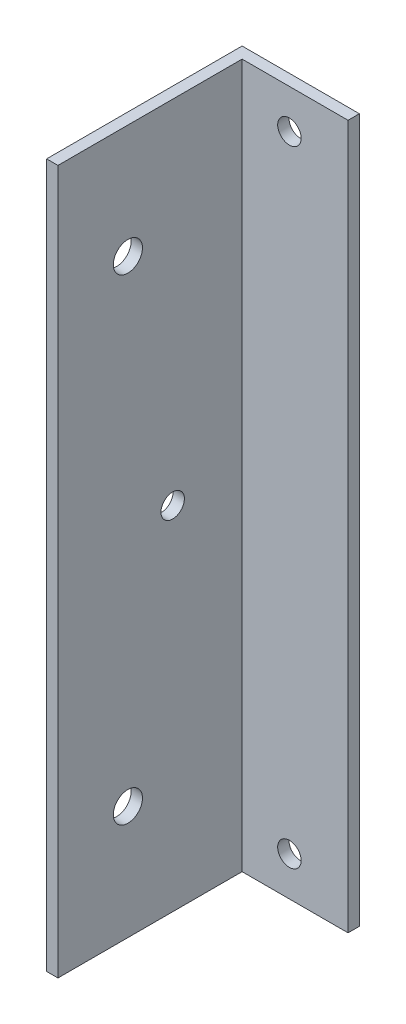
SolidWorks part; units mm, degrees
ref_plane "Front Plane" through (0, 0, 0) normal (0, 0, 1) x (1, 0, 0)
ref_plane "Top Plane" through (0, 0, 0) normal (0, 1, 0) x (1, 0, 0)
ref_plane "Right Plane" through (0, 0, 0) normal (1, 0, 0) x (0, 0, -1)
sketch "Sketch1" plane through (0, 0, 0) normal (0, 0, 1) x (1, 0, 0)
  line L1 (-7.5, 45) -> (7.5, 45)
  line L2 (-7.5, 45) -> (-7.5, -45)
  line L3 (-7.5, -45) -> (7.5, -45)
  line L4 (7.5, 45) -> (7.5, -45)
  line L5 (-7.5, 45) -> (7.5, -45) construction
  line L6 (-7.5, -45) -> (7.5, 45) construction
  point P0 (0, 0)
  dimension "D1" = 15
  dimension "D2" = 90
extrude "Boss-Extrude1" add sketch "Sketch1" along normal blind 1.45
sketch "Sketch2" plane through (0, 0, 1.45) normal (0, 0, 1) x (1, 0, 0)
  line L0 (-7.5, -45) -> (7.5, -45) construction
  line L1 (-7.5, 45) -> (-6.05, 45)
  line L2 (-7.5, 45) -> (-7.5, -45)
  line L3 (-7.5, -45) -> (-6.05, -45)
  line L4 (-6.05, 45) -> (-6.05, -45)
  dimension "D1" = 1.45
extrude "Boss-Extrude2" add sketch "Sketch2" along normal blind 23.55
sketch "Sketch3" plane through (0, 0, 0) normal (0, 0, -1) x (-1, 0, 0)
  line L0 (-7.5, 45) -> (7.5, 45) construction
  line L1 (7.5, -45) -> (-7.5, -45) construction
  circle A0 centre (0, 40) radius 1.5
  circle A1 centre (0, -40) radius 1.5
  point P8 (0, 0)
  dimension "D1" = 3
  dimension "D2" = 3
  dimension "D3" = 5
  dimension "D4" = 5
extrude "Cut-Extrude1" cut sketch "Sketch3" against normal through all
sketch "Sketch5" plane through (-7.5, 0, 0) normal (-1, 0, 0) x (0, 0, 1)
  line L0 (25, 45) -> (25, -45) construction
  line L1 (25, -45) -> (0, -45) construction
  circle A0 centre (16.057, -30.462) radius 1.865
  dimension "D1" = 3.73
  dimension "D2" = 8.943
  dimension "D3" = 14.538
extrude "Cut-Extrude2" cut sketch "Sketch5" against normal up to next (1.45 mm away)
mirror "Mirror1" about plane through (0, 0, 0) normal (0, 1, 0) of "Cut-Extrude2"
sketch "Sketch6" plane through (-7.5, 0, 0) normal (-1, 0, 0) x (0, 0, 1)
  line L0 (25, 45) -> (25, -45) construction
  circle A0 centre (10.33, 0) radius 1.5
  point P4 (0, 0)
  dimension "D1" = 3
  dimension "D2" = 14.67
extrude "Cut-Extrude3" cut sketch "Sketch6" against normal up to next
